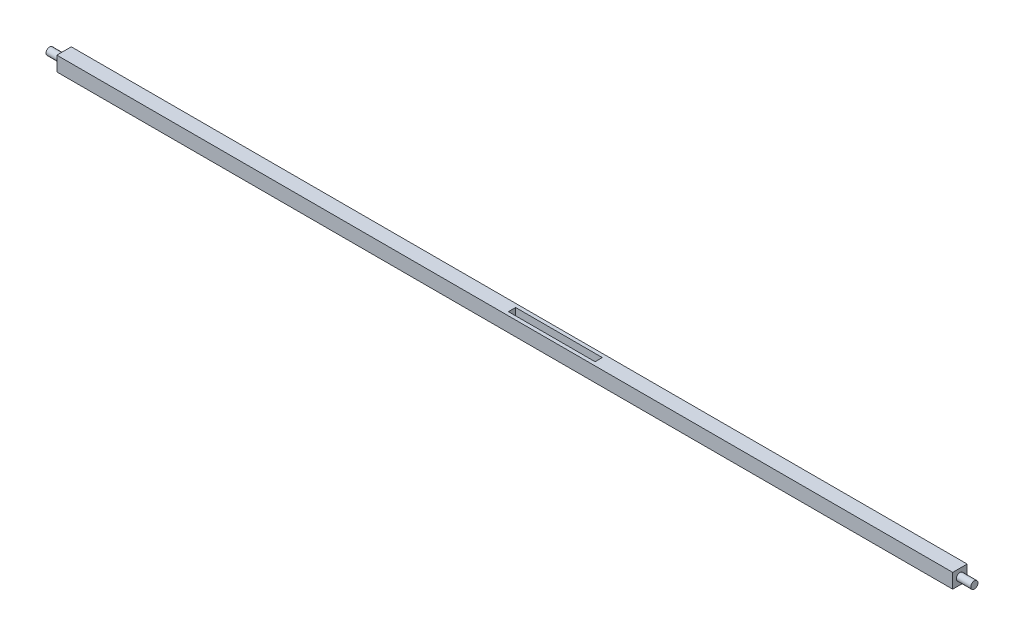
SolidWorks part; units mm, degrees
material "6061-T6 (SS)"
ref_plane "Front Plane" through (0, 0, 0) normal (0, 0, 1) x (1, 0, 0)
ref_plane "Top Plane" through (0, 0, 0) normal (0, 1, 0) x (1, 0, 0)
ref_plane "Right Plane" through (0, 0, 0) normal (1, 0, 0) x (0, 0, -1)
sketch "Sketch1" plane through (0, 0, 0) normal (1, 0, 0) x (0, 0, -1)
  line L1 (-6.35, -6.4107) -> (6.35, -6.4107)
  line L2 (-6.35, -6.4107) -> (-6.35, 6.4107)
  line L3 (-6.35, 6.4107) -> (6.35, 6.4107)
  line L4 (6.35, -6.4107) -> (6.35, 6.4107)
  line L5 (-6.35, -6.4107) -> (6.35, 6.4107) construction
  line L6 (-6.35, 6.4107) -> (6.35, -6.4107) construction
  point P0 (0, 0)
  dimension "D1" = 12.7
  dimension "D2" = 12.8213
extrude "Length" add sketch "Sketch1" along normal mid plane 812.8
ref_plane "Top" through (406.4, 0, 0) normal (1, 0, 0) x (0, 0, -1)
sketch "Sketch2" plane through (406.4, 0, 0) normal (1, 0, 0) x (0, 0, -1)
  line L5 (-2.2344, -2.2557) -> (2.2344, 2.2557) construction
  line L6 (-2.2344, 2.2557) -> (2.2344, -2.2557) construction
  line L7 (-6.35, -6.4107) -> (6.35, -6.4107)
  line L8 (-6.35, -6.4107) -> (-6.35, 6.4107)
  line L9 (-6.35, 6.4107) -> (6.35, 6.4107)
  line L10 (6.35, -6.4107) -> (6.35, 6.4107)
  line L11 (-6.35, -6.4107) -> (6.35, 6.4107) construction
  line L12 (-6.35, 6.4107) -> (6.35, -6.4107) construction
  circle A0 centre (0, 0) radius 3.175
  point P0 (0, 0)
  dimension "D1" = 6.35
extrude "Round Cut 1" cut sketch "Sketch2" against normal blind 12.7 contours L7 L10 L9 L8 A0
ref_plane "Bottom Plane" through (-406.4, 0, 0) normal (-1, 0, 0) x (0, 0, 1)
sketch "Sketch3" plane through (-406.4, 0, 0) normal (-1, 0, 0) x (0, 0, 1)
  line L1 (-6.35, -6.4107) -> (6.35, -6.4107)
  line L2 (-6.35, -6.4107) -> (-6.35, 6.4107)
  line L3 (-6.35, 6.4107) -> (6.35, 6.4107)
  line L4 (6.35, -6.4107) -> (6.35, 6.4107)
  line L5 (-6.35, -6.4107) -> (6.35, 6.4107) construction
  line L6 (-6.35, 6.4107) -> (6.35, -6.4107) construction
  circle A0 centre (0, 0) radius 3.175
  point P0 (0, 0)
  dimension "D1" = 6.35
extrude "Round Cut 2" cut sketch "Sketch3" against normal blind 12.7 contours L1 L4 L3 L2 A0
ref_plane "Plane1" through (0, 6.4107, 0) normal (0, 1, 0) x (1, 0, 0)
sketch "Sketch5" plane through (0, 6.4107, 0) normal (0, 1, 0) x (1, 0, 0)
  line L1 (0, 3.175) -> (76.2, 3.175)
  line L2 (0, 3.175) -> (0, -3.175)
  line L3 (0, -3.175) -> (76.2, -3.175)
  line L4 (76.2, 3.175) -> (76.2, -3.175)
  line L5 (-406.4, 3.4925) -> (-406.4, -3.4925) construction
  point P4 (76.2, 0)
  dimension "D1" = 76.2
  dimension "D2" = 6.35
  dimension "D3" = 0
  dimension "D4" = 406.4
extrude "Cut-Extrude1" cut sketch "Sketch5" against normal up to next
equation "\"Diameter\"= .25"
equation "\"Round Cut Depth Top\"= .5"
equation "\"Stringer Length\"= 32"
equation "\"D1@Sketch3\"= \"Diameter\""
equation "\"D1@Sketch2\"= \"Diameter\""
equation "\"D1@Round Cut 1\"= \"Round Cut Depth Top\""
equation "\"D1@Round Cut 2\" = \"Round Cut Depth Bottom\""
equation "\"D1@Length\"= \"Stringer Length\""
equation "\"Round Cut Depth Bottom\"= .5"
